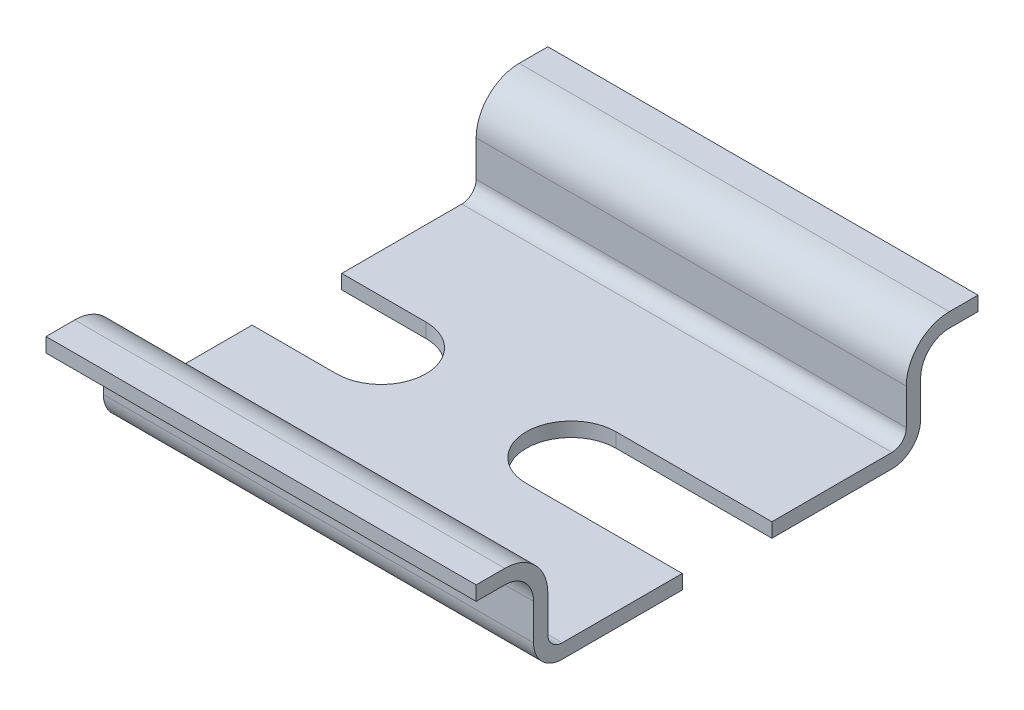
SolidWorks part; units mm, degrees
ref_plane "Front Plane" through (0, 0, 0) normal (0, 0, 1) x (1, 0, 0)
ref_plane "Top Plane" through (0, 0, 0) normal (0, 1, 0) x (1, 0, 0)
ref_plane "Right Plane" through (0, 0, 0) normal (1, 0, 0) x (0, 0, -1)
sketch "Sketch1" plane through (0, 0, 0) normal (1, 0, 0) x (0, 0, -1)
  line L0 (0, 0) -> (0, 18.2344) construction
  line L1 (0, 0) -> (26.621, 0) construction
  line L2 (-11.5, 0) -> (11.5, 0)
  line L3 (13.5, 2) -> (13.5, 4.5)
  line L4 (15.5, 6.5) -> (17.5, 6.5)
  line L5 (-13.5, 2) -> (-13.5, 4.5)
  line L6 (-15.5, 6.5) -> (-17.5, 6.5)
  arc A0 (13.5, 2) -> (11.5, 0) centre (11.5, 2) cw
  arc A1 (15.5, 6.5) -> (13.5, 4.5) centre (15.5, 4.5) ccw
  arc A2 (-13.5, 2) -> (-11.5, 0) centre (-11.5, 2) ccw
  arc A3 (-15.5, 6.5) -> (-13.5, 4.5) centre (-15.5, 4.5) cw
  point P9 (13.5, 0)
  dimension "D1" = 2
  dimension "D3" = 2
  dimension "D2" = 6.5
  dimension "D4" = 35
  dimension "D5" = 27
extrude "Extrude-Thin1" add sketch "Sketch1" along normal blind 30 thin thin type one direction wall 1
sketch "Sketch2" plane through (0, 0, 0) normal (0, -1, 0) x (1, 0, 0)
  line L0 (0, 6.6969) -> (0, 0) construction
  line L1 (0, 0) -> (9.9599, 0) construction
  line L2 (-5.875, 3.125) -> (5.875, 3.125)
  line L3 (-5.875, -3.125) -> (5.875, -3.125)
  arc A0 (5.875, 3.125) -> (5.875, -3.125) centre (5.875, 0) cw
  arc A1 (-5.875, 3.125) -> (-5.875, -3.125) centre (-5.875, 0) ccw
  point P6 (0, 3.125)
  point P12 (0, -3.125)
  dimension "D2" = 11.75
  dimension "D1" = 6.25
extrude "Cut-Extrude1" cut sketch "Sketch2" against normal up to next (1 mm away)
pattern_linear "LPattern1" count 2 spacing 25 along (1, 0, 0) of "Cut-Extrude1"
equation "\"length\"= 30mm"
equation "\"D1@Extrude-Thin1\"=\"length\""
equation "\"holes\"= \"length\" / 25 + 1"
equation "\"D1@LPattern1\"=\"holes\""
